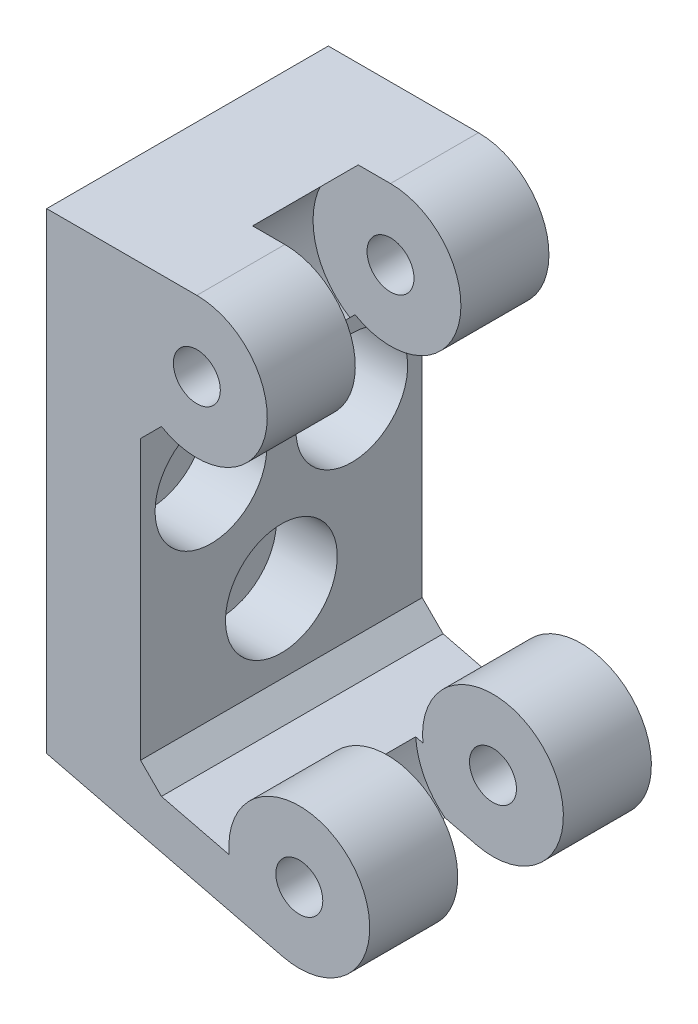
SolidWorks part; units mm, degrees
other "Markup1"
sketch "Sketch3" plane through (0, 0, 12) normal (0, 0, 1) x (1, 0, 0)
other "DetailItem1"
other "DetailItem3"
other "DetailItem5"
ref_plane "Front Plane" through (0, 0, 0) normal (0, 0, 1) x (1, 0, 0)
ref_plane "Top Plane" through (0, 0, 0) normal (0, 1, 0) x (1, 0, 0)
ref_plane "Right Plane" through (0, 0, 0) normal (1, 0, 0) x (0, 0, -1)
sketch "Sketch-optimization parameters" plane through (0, 0, 0) normal (0, 0, 1) x (1, 0, 0)
  line L2 (0, 0) -> (0, 20.1035)
  line L3 (0, 20.1035) -> (6.3989, 20.1035)
  line L5 (4.8896, 14.5108) -> (4, 13.6212)
  line L6 (4, 13.6212) -> (4, 1.7504)
  line L7 (4.8896, 0.8608) -> (7.7788, 0.1528)
  line L11 (6.3989, 17.1035) -> (10.764, 0.4507) construction
  line L16 (3.444, 0.5146) -> (10.764, 0.4507) construction
  line L17 (6.3989, -983.3033) -> (6.3989, 49016.6967) construction
  line L22 (4, 1.7504) -> (4.8896, 0.8608)
  line L23 (0, 0) -> (10.0499, -2.463)
  line L28 (-1000, 0) -> (49000, 0) construction
  line L29 (0, -1000) -> (0, 49000) construction
  line L30 (6.3655, 16.9158) -> (-8761.9708, -49208.2432) construction
  line L31 (-993.9512, 17.1035) -> (49006.0488, 17.1035) construction
  arc A0 (10.0499, -2.463) -> (7.7788, 0.1528) centre (10.764, 0.4507) ccw
  arc A1 (6.3989, 20.1035) -> (4.8896, 14.5108) centre (6.3989, 17.1035) cw
  circle A2 centre (6.3989, 17.1035) radius 1
  circle A3 centre (10.764, 0.4507) radius 1
  dimension "D1" = 2
  dimension "D3" = 3
  dimension "D2" = 4
  dimension "D4" = 16.85
  dimension "D5" = 79.9
  dimension "D6" = 99.6
  dimension "D7" = 7.32
  dimension "D8" = 2
  dimension "D9" = 135
  dimension "D10" = 135
extrude "Boss-Extrude1" add sketch "Sketch-optimization parameters" along normal blind 12
ref_plane "midplane" through (0, 0, 6) normal (0, 0, 1) x (1, 0, 0)
sketch "Sketch2" plane through (0, 0, 6) normal (0, 0, 1) x (1, 0, 0)
  circle A0 centre (6.3989, 17.1035) radius 3.3
  circle A1 centre (10.764, 0.4507) radius 3.3
  dimension "D1" = 6.6
extrude "Cut-Extrude1" cut sketch "Sketch2" against normal blind 2.25 and the other way blind 2.25
ref_plane "Plane - base" [suppressed] through (-6.9825, 2.8211, 0) normal (-0.9272, 0.3746, 0) x (0, 0, -1)
sketch "Sketch4" [suppressed] plane through (-6.9825, 2.8211, 0) normal (-0.9272, 0.3746, 0) x (0, 0, -1)
  line L1 (-12, -18.6396) -> (0, -18.6396)
  line L2 (-12, -18.6396) -> (-12, 0)
  line L3 (-12, 0) -> (0, 0)
  line L4 (0, -18.6396) -> (0, 0)
extrude "Boss-Extrude2" [suppressed] add sketch "Sketch4" against normal up to surface
sketch "Hole sketch" plane through (4, 36.4446, 0) normal (-1, 0, 0) x (0, 0, -1)
  line L0 (-12, 25.8234) -> (0, 25.8234) construction
  line L3 (-6, -1.7766) -> (-6, 49998.2234) construction
  line L4 (-6, 44.0148) -> (-6, 28.8745) construction
  line L5 (-12, 28.8234) -> (-12, 22.8234) construction
  line L6 (-12, 17.9286) -> (-12, 44.7815) construction
  line L7 (-12, 31.3551) -> (-6, 31.3551) construction
  line L8 (0, 16.3411) -> (0, 36.4446) construction
  line L9 (-12, 22.8234) -> (0, 22.8234) construction
  line L10 (-12, 22.8234) -> (0, 22.8234) construction
  circle A0 centre (-9, 25.8234) radius 1.2884
  circle A1 centre (-3, 25.8234) radius 1.2884
  circle A2 centre (-6, 31.3551) radius 1.2884
  point P8 (-9, 25.8234)
  point P9 (-3, 25.8234)
  point P10 (-6, 31.3551)
  dimension "D2" = 2.5768
  dimension "D1" = 3
  dimension "D3" = 3
extrude "Screw shaft holes" cut sketch "Hole sketch" against normal through all both and the other way through all
sketch "Sketch5" plane through (4, 26.1971, 0) normal (-1, 0, 0) x (0, 0, -1)
  circle A0 centre (-6, 21.1076) radius 2.3813
  circle A1 centre (-9, 15.5759) radius 2.3813
  circle A2 centre (-3, 15.5759) radius 2.3813
  dimension "D1" = 4.7625
extrude "Screw counterbores" cut sketch "Sketch5" along normal blind 2.5918
equation "\"axle-diameter\"=2"
equation "\"D1@Sketch-optimization parameters\" = \"axle-diameter\""
equation "\"switch-thickness\"=12"
equation "\"D1@Boss-Extrude1\"=\"switch-thickness\""
equation "\"base-width\"=4.0"
equation "\"axle-bushing-radius\"=3"
equation "\"D3@Sketch-optimization parameters\" = \"axle-bushing-radius\""
equation "\"D1@Sketch2\"=\"axle-bushing-radius\"*2.2"
equation "\"D1@Cut-Extrude1\"=\"switch-thickness\"/6+\"clearance\""
equation "\"D2@Cut-Extrude1\"=\"switch-thickness\"/6+\"clearance\""
equation "\"clearance\"= 0.25"
equation "\"arm-width\"=3.0"
equation "\"min-diameter\"=70"
